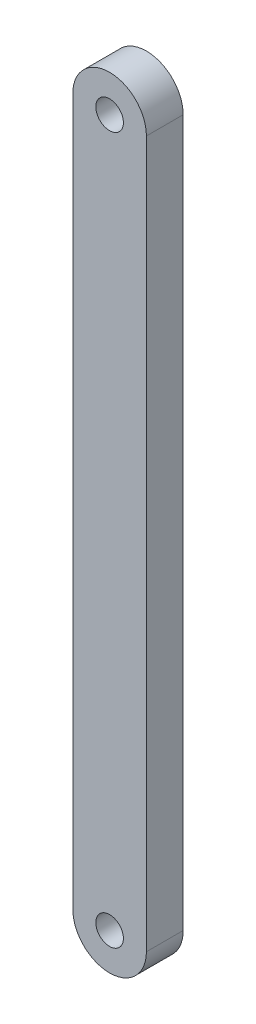
SolidWorks part; units mm, degrees
ref_plane "Front Plane" through (0, 0, 0) normal (0, 0, 1) x (1, 0, 0)
ref_plane "Top Plane" through (0, 0, 0) normal (0, 1, 0) x (1, 0, 0)
ref_plane "Right Plane" through (0, 0, 0) normal (1, 0, 0) x (0, 0, -1)
sketch "Sketch1" plane through (0, 0, 0) normal (0, 0, 1) x (1, 0, 0)
  line L0 (0, 121.92) -> (0, -121.92) construction
  line L1 (12.7, 121.92) -> (12.7, -121.92)
  line L2 (-12.7, 121.92) -> (-12.7, -121.92)
  arc A0 (12.7, 121.92) -> (-12.7, 121.92) centre (0, 121.92) ccw
  arc A1 (-12.7, -121.92) -> (12.7, -121.92) centre (0, -121.92) ccw
  circle A2 centre (0, 121.92) radius 4.7625
  circle A3 centre (0, -121.92) radius 4.7625
  point P3 (0, 0)
  dimension "D2" = 9.525
  dimension "D1" = 243.84
  dimension "D3" = 25.4
extrude "Boss-Extrude1" add sketch "Sketch1" along normal blind 12.7
